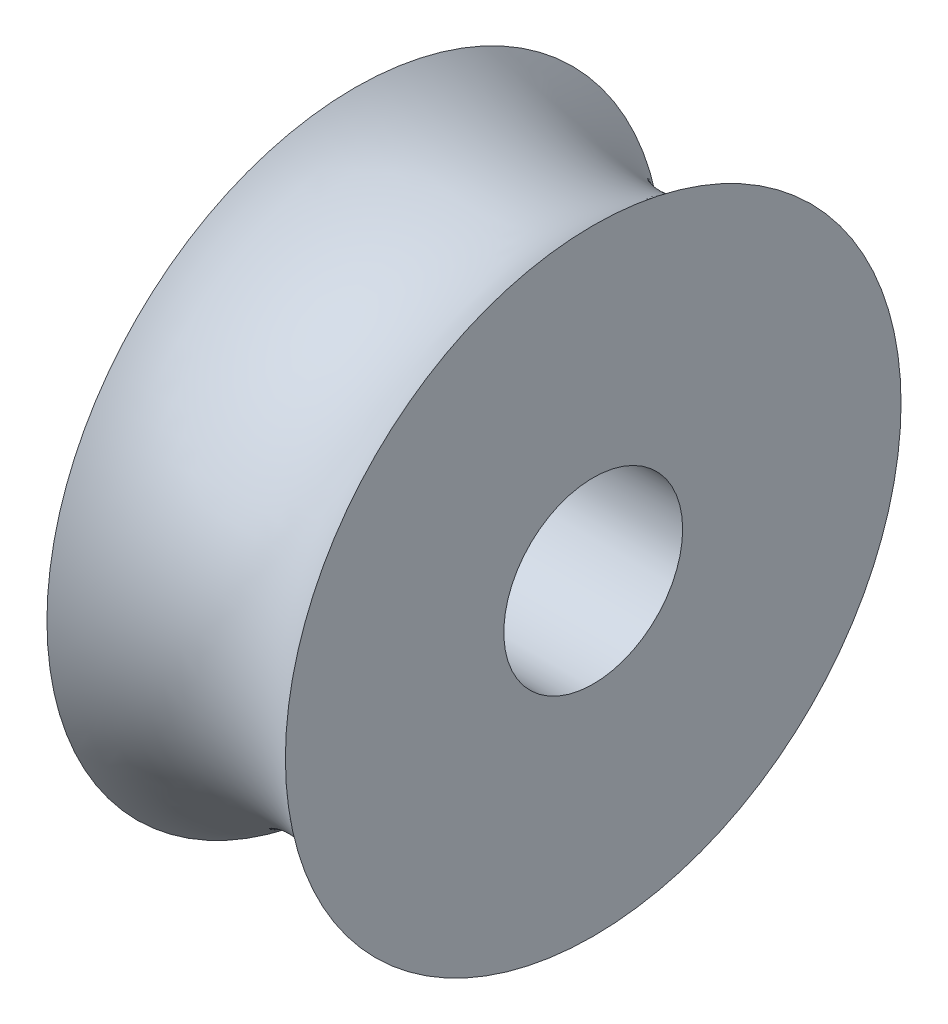
SolidWorks part; units mm, degrees
ref_plane "Front Plane" through (0, 0, 0) normal (0, 0, 1) x (1, 0, 0)
ref_plane "Top Plane" through (0, 0, 0) normal (0, 1, 0) x (1, 0, 0)
ref_plane "Right Plane" through (0, 0, 0) normal (1, 0, 0) x (0, 0, -1)
sketch "Sketch1" plane through (0, 0, 0) normal (0, 0, 1) x (1, 0, 0)
  line L0 (-3.175, 0) -> (3.175, 0)
  line L1 (3.175, 0) -> (3.175, 8.1977)
  line L2 (-3.175, 0) -> (-3.175, 8.1977)
  arc A0 (-3.175, 8.1977) -> (3.175, 8.1977) centre (0, 11.7475) ccw
  point P8 (0, 6.985)
  dimension "D4" = 4.7625
  dimension "D1" = 6.985
  dimension "D2" = 3.175
  dimension "D3" = 3.175
revolve "Revolve1" add sketch "Sketch1" angle 360 about L0
sketch "Sketch2" plane through (3.175, 0, 0) normal (1, 0, 0) x (0, 0, -1)
  circle A0 centre (0, 0) radius 2.3813
  dimension "D1" = 4.7625
extrude "Cut-Extrude1" cut sketch "Sketch2" against normal through all
